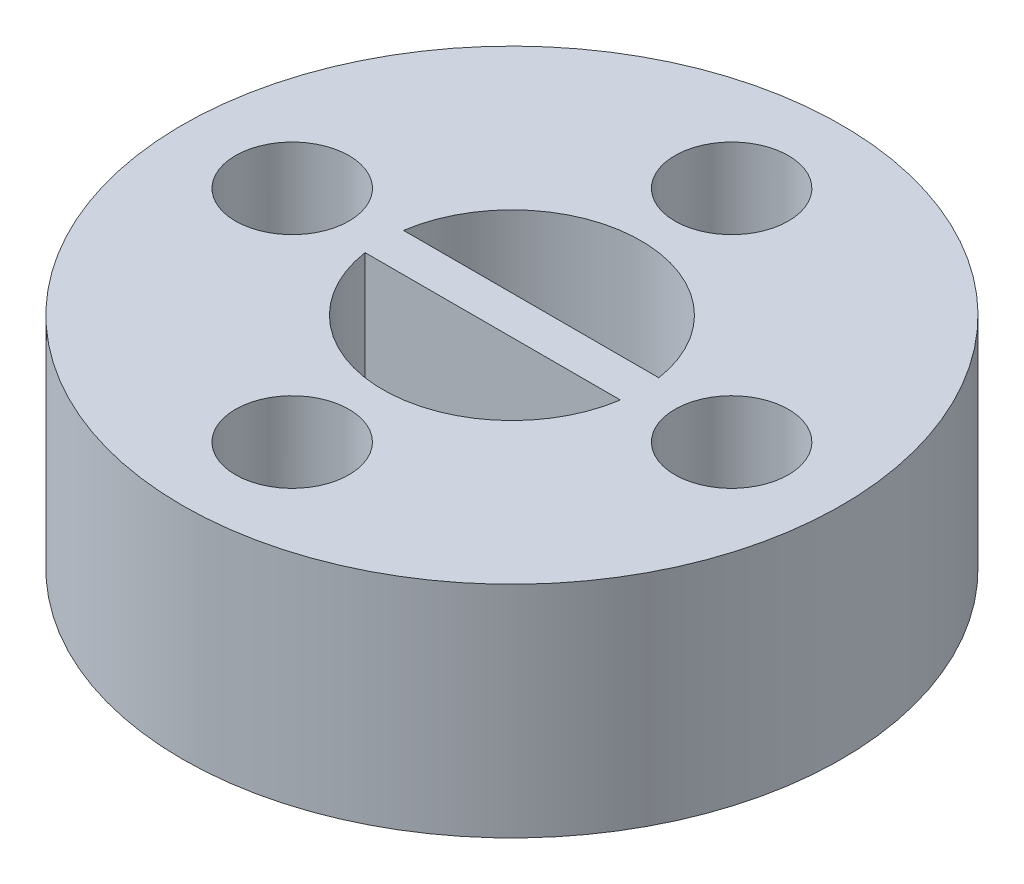
SolidWorks part; units mm, degrees
ref_plane "Front Plane" through (0, 0, 0) normal (0, 0, 1) x (1, 0, 0)
ref_plane "Top Plane" through (0, 0, 0) normal (0, 1, 0) x (1, 0, 0)
ref_plane "Right Plane" through (0, 0, 0) normal (1, 0, 0) x (0, 0, -1)
sketch "Sketch1" plane through (0, 0, 0) normal (0, 1, 0) x (1, 0, 0)
  circle A0 centre (0, 0) radius 3.525
  circle A1 centre (0, 0) radius 9
  dimension "D1" = 7.05
  dimension "D2" = 18
extrude "Boss-Extrude1" add sketch "Sketch1" along normal blind 6
sketch "Sketch2" plane through (0, 0, 0) normal (0, 1, 0) x (1, 0, 0)
  line L0 (-3.525, 0) -> (3.525, 0) construction
  line L1 (-3.525, 0.525) -> (3.525, 0.525)
  line L2 (-3.525, 0.525) -> (-3.525, -0.525)
  line L3 (3.525, 0.525) -> (3.525, -0.525)
  line L4 (-3.525, -0.525) -> (3.525, -0.525)
  line L5 (3.525, 0) -> (-3.525, 0) construction
  line L6 (0, 0.525) -> (0, -0.525) construction
  circle A0 centre (0, 0) radius 3.525 construction
  point P5 (0, 0)
  point P6 (0, 0)
  dimension "D1" = 1.05
extrude "Boss-Extrude2" add sketch "Sketch2" along normal blind 6
sketch "Sketch3" plane through (0, 6, 0) normal (0, 1, 0) x (1, 0, 0)
  line L0 (0, 0) -> (6, 0) construction
  circle A0 centre (6, 0) radius 1.55
  dimension "D1" = 3.1
  dimension "D2" = 6
extrude "Cut-Extrude1" cut sketch "Sketch3" against normal blind 8
pattern_circular "CirPattern1" count 4 over 360 about axis through (0, 0, 0) along (0, 1, 0) of "Cut-Extrude1"
